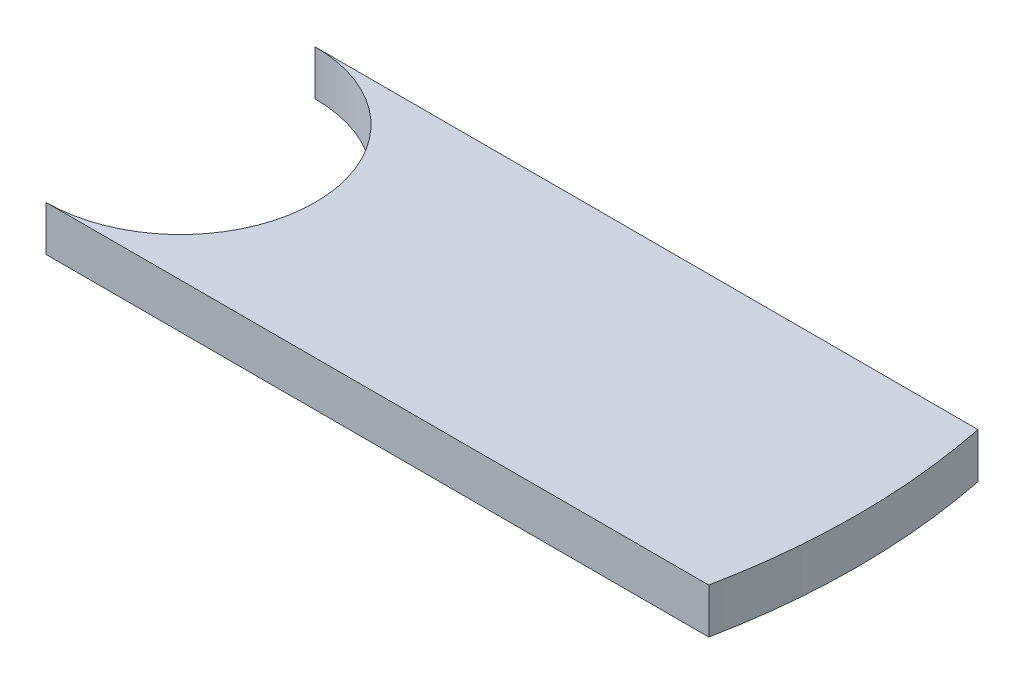
SolidWorks part; units mm, degrees
material "Lead"
ref_plane "Front" through (0, 0, 0) normal (0, 0, 1) x (1, 0, 0)
ref_plane "Top" through (0, 0, 0) normal (0, 1, 0) x (1, 0, 0)
ref_plane "Right" through (0, 0, 0) normal (1, 0, 0) x (0, 0, -1)
sketch "Sketch1" plane through (0, 0, 0) normal (0, 1, 0) x (1, 0, 0)
  line L3 (0, -26.575) -> (130.8282, -26.575)
  line L7 (0, 26.575) -> (130.8282, 26.575)
  arc A0 (133.5, 0) -> (130.8282, -26.575) centre (0, 0) cw
  arc A1 (0, -26.575) -> (0, 26.575) centre (0, 0) ccw
  arc A2 (133.5, 0) -> (130.8282, 26.575) centre (0, 0) ccw
extrude "Boss-Extrude1" add sketch "Sketch1" along normal blind 8.9 contours L3 A0 A2 L7 A1
